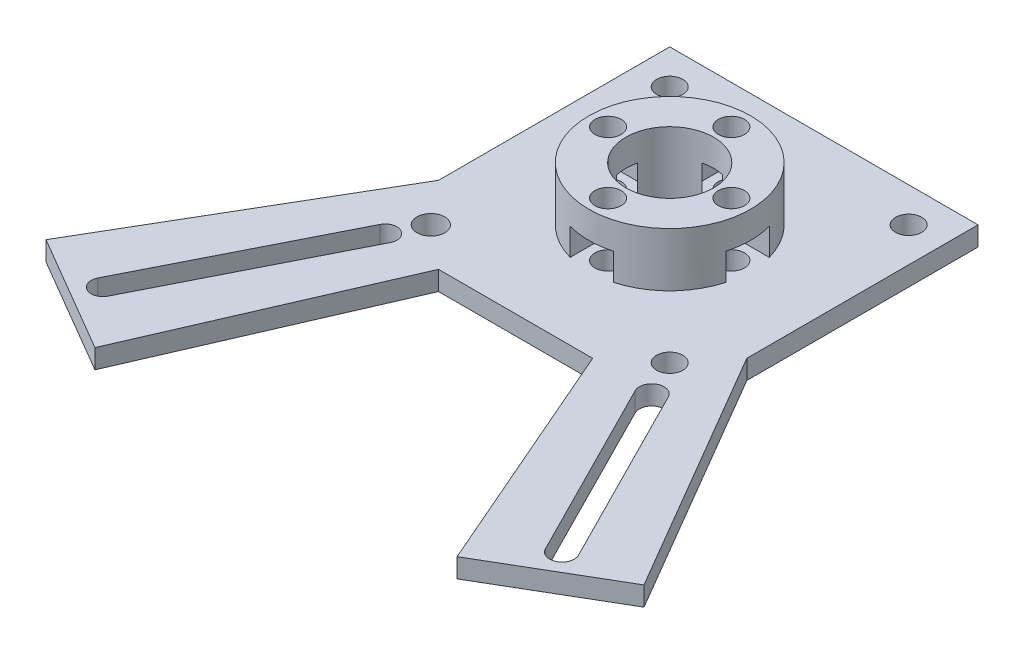
SolidWorks part; units mm, degrees
ref_plane "前视基准面" through (0, 0, 0) normal (0, 0, 1) x (1, 0, 0)
ref_plane "上视基准面" through (0, 0, 0) normal (0, 1, 0) x (1, 0, 0)
ref_plane "右视基准面" through (0, 0, 0) normal (1, 0, 0) x (0, 0, -1)
sketch "草图1" plane through (0, 0, 0) normal (0, 1, 0) x (1, 0, 0)
  line L3 (-9.9994, -20.0003) -> (10.0006, -20.0003)
  line L6 (-20, -10) -> (-38.7957, -42.1354)
  line L7 (10.0006, -20.0003) -> (23.4932, -51.0857)
  line L8 (20, -10) -> (38.796, -42.135)
  line L9 (-15.5, -15.5) -> (-31.1994, -46.5784) construction
  line L10 (15.5, -15.5) -> (31.1994, -46.5783) construction
  line L11 (-38.7957, -42.1354) -> (-23.4932, -51.0857)
  line L12 (-17.4886, -19.4366) -> (-29.776, -43.7606) construction
  line L13 (-16.1319, -20.122) -> (-28.4192, -44.4459)
  line L14 (-18.8453, -18.7513) -> (-31.1327, -43.0752)
  line L15 (17.824, -20.1595) -> (29.776, -43.7606) construction
  line L16 (19.2514, -19.4366) -> (31.2034, -43.0377)
  line L17 (16.3966, -20.8823) -> (28.3486, -44.4834)
  line L20 (-9.9994, -20.0003) -> (-23.4932, -51.0857)
  line L21 (-20, -10) -> (-20, 20)
  line L22 (23.4932, -51.0857) -> (38.796, -42.135)
  line L23 (-20, 20) -> (20, 20)
  line L24 (20, 20) -> (20, -10)
  circle A0 centre (15.5, 15.5) radius 1.7
  circle A2 centre (-15.5, -15.5) radius 1.8
  circle A4 centre (-15.5, 15.5) radius 1.7
  arc A6 (-16.1319, -20.122) -> (-18.8453, -18.7513) centre (-17.4886, -19.4366) ccw
  arc A7 (-31.1327, -43.0752) -> (-28.4192, -44.4459) centre (-29.776, -43.7606) ccw
  circle A8 centre (0, 0) radius 5.7
  circle A9 centre (-8, 0) radius 1.7
  circle A10 centre (0, 8) radius 1.7
  circle A11 centre (8, 0) radius 1.7
  circle A12 centre (0, -8) radius 1.7
  arc A13 (19.2514, -19.4366) -> (16.3966, -20.8823) centre (17.824, -20.1595) ccw
  arc A14 (28.3486, -44.4834) -> (31.2034, -43.0377) centre (29.776, -43.7606) ccw
  circle A15 centre (15.5, -15.5) radius 1.7
  point P34 (-33.1606, -34.0237)
  point P38 (-23.6323, -31.5986)
  point P43 (23.8, -31.96)
extrude "凸台-拉伸1" add sketch "草图1" along normal blind 2.5
sketch "草图2" plane through (0, 2.5, 0) normal (0, 1, 0) x (1, 0, 0)
  circle A0 centre (0, 0) radius 10.5
extrude "凸台-拉伸2" add sketch "草图2" along normal blind 7
sketch "草图4" plane through (0, 2.5, 0) normal (0, -1, 0) x (1, 0, 0)
  circle A1 centre (0, -8) radius 1.7
  circle A2 centre (-8, 0) radius 1.7
  circle A3 centre (8, 0) radius 1.7
  circle A4 centre (0, 8) radius 1.7
extrude "切除-拉伸1" cut sketch "草图4" against normal blind 7
sketch "草图5" plane through (0, 2.5, 0) normal (0, 1, 0) x (1, 0, 0)
  line L1 (-4.7668, 0) -> (-6.3834, 2.8)
  line L2 (-6.3834, 2.8) -> (-11.2332, 2.8)
  line L5 (-11.2332, -2.8) -> (-6.3834, -2.8)
  line L6 (-6.3834, -2.8) -> (-4.7668, 0)
  line L7 (4.7668, 0) -> (6.3834, -2.8)
  line L8 (6.3834, -2.8) -> (11.2332, -2.8)
  line L11 (11.2332, 2.8) -> (6.3834, 2.8)
  line L12 (6.3834, 2.8) -> (4.7668, 0)
  line L14 (-2.8, 11.2332) -> (-2.8, 6.3834)
  line L15 (-2.8, 6.3834) -> (0, 4.7668)
  line L16 (0, 4.7668) -> (2.8, 6.3834)
  line L17 (2.8, 6.3834) -> (2.8, 11.2332)
  line L19 (0, -4.7668) -> (-2.8, -6.3834)
  line L20 (-2.8, -6.3834) -> (-2.8, -11.2332)
  line L23 (2.8, -11.2332) -> (2.8, -6.3834)
  line L24 (2.8, -6.3834) -> (0, -4.7668)
  line L25 (-11.2332, 2.8) -> (-11.2332, -2.8)
  line L29 (-2.8, 11.2332) -> (2.8, 11.2332)
  line L32 (11.2332, 2.8) -> (11.2332, -2.8)
  line L35 (-2.8, -11.2332) -> (2.8, -11.2332)
  line L39 (-1.4, -10.4249) -> (0, -11.2332) [skipped]
  line L40 (1.4, -10.4249) -> (2.8, -9.6166) [skipped]
  line L41 (9.6166, -2.8) -> (10.4249, -1.4) [skipped]
  line L42 (11.2332, 0) -> (10.4249, 1.4) [skipped]
  line L43 (1.4, 10.4249) -> (0, 11.2332) [skipped]
  line L44 (0, 11.2332) -> (-1.4, 10.4249) [skipped]
  line L45 (-10.4249, -1.4) -> (-9.6166, -2.8) [skipped]
  line L46 (-9.6166, 2.8) -> (-10.4249, 1.4) [skipped]
extrude "切除-拉伸2" cut sketch "草图5" along normal blind 3.5
sketch "草图6" plane through (0, 2.5, 0) normal (0, -1, 0) x (1, 0, 0)
  circle A0 centre (0, 0) radius 5.7
extrude "切除-拉伸3" cut sketch "草图6" against normal blind 20
